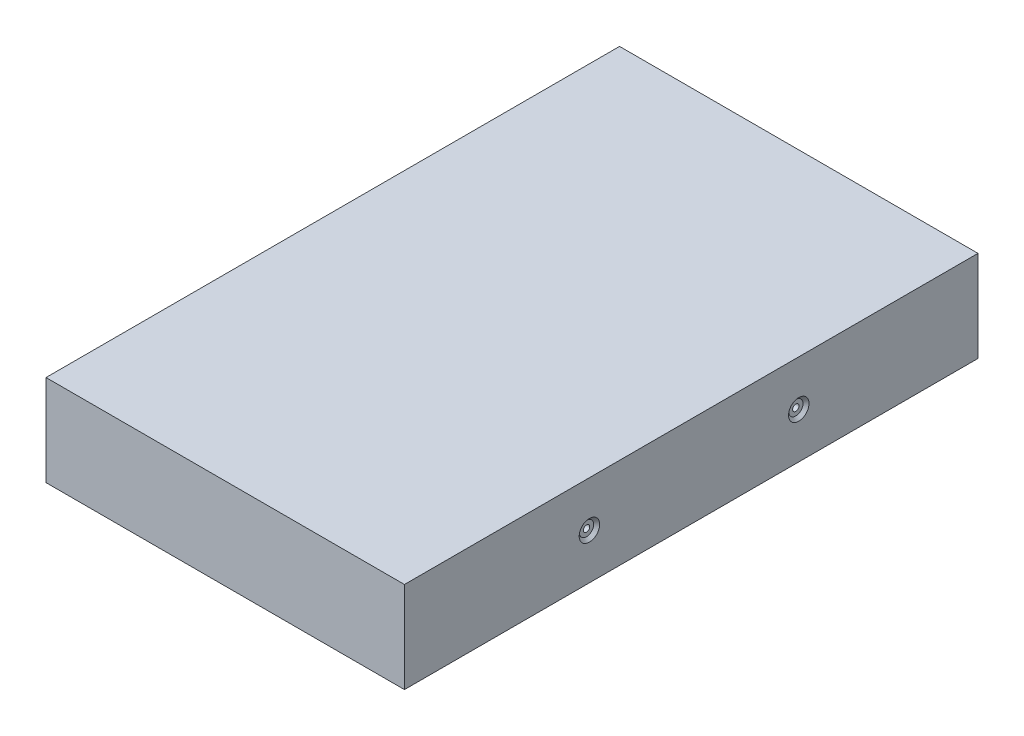
SolidWorks part; units mm, degrees
ref_plane "Front Plane" through (0, 0, 0) normal (0, 0, 1) x (1, 0, 0)
ref_plane "Top Plane" through (0, 0, 0) normal (0, 1, 0) x (1, 0, 0)
ref_plane "Right Plane" through (0, 0, 0) normal (1, 0, 0) x (0, 0, -1)
sketch "Sketch1" plane through (0, 0, 0) normal (0, 1, 0) x (1, 0, 0)
  line L1 (-50, 80) -> (50, 80)
  line L2 (-50, 80) -> (-50, -80)
  line L3 (-50, -80) -> (50, -80)
  line L4 (50, 80) -> (50, -80)
  line L5 (-50, 80) -> (50, -80) construction
  line L6 (-50, -80) -> (50, 80) construction
  point P0 (0, 0)
  dimension "D1" = 100
  dimension "D2" = 160
extrude "Boss-Extrude1" add sketch "Sketch1" along normal blind 25.4
hole_wizard "CBORE for #0 Binding Head Machine Screw1" positions "Sketch2" profile "Sketch3" counterbore size "#0" standard "ANSI Inch"
sketch "Sketch2" plane through (50, 0, 0) normal (1, 0, 0) x (0, 0, -1)
  line L0 (-80, 0) -> (80, 0) construction
  line L2 (80, 25.4) -> (80, 0) construction
  point P0 (-28.4, 12.7)
  point P2 (30, 12.7)
  dimension "D1" = 12.7
  dimension "D2" = 58.4
  dimension "D3" = 50
sketch "Sketch3" plane through (50, 12.7, 28.4) normal (0, 1, 0) x (0, 0, -1)
  line L0 (0, 0) -> (0, 30.5342)
  line L1 (0, 30.5342) -> (0.889, 30)
  line L2 (0.889, 30) -> (0.889, 0.8128)
  line L3 (0.889, 0.8128) -> (1.985, 0.8128)
  line L5 (1.985, 0.8128) -> (1.985, 0.8725)
  line L6 (1.985, 0.8725) -> (2.8575, 0)
  line L7 (2.8575, 0) -> (0, 0)
  line L8 (-1.985, 0.8725) -> (-2.8575, 0) construction
  line L10 (0, 30.5342) -> (-0.889, 30) construction
  line L11 (0, -6.35) -> (0, 107.95) construction
  dimension "Hole Dia." = 1.778
  dimension "Hole Depth" = 30
  dimension "C'Bore Dia." = 3.97
  dimension "C'Bore Depth" = 0.8128
  dimension "Near C'Sink Dia." = 5.715
  dimension "Near C'Sink Angle" = 90
  dimension "Drill Angle" = 118
